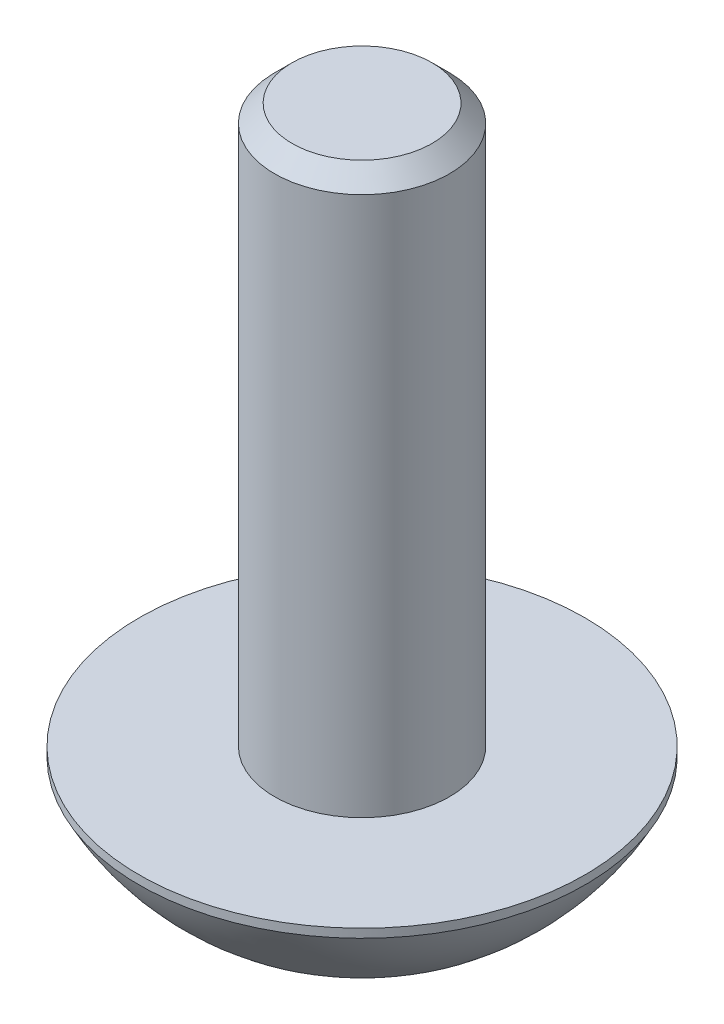
SolidWorks part; units mm, degrees
material "1.4301 (X5CrNi18-10)"
ref_plane "Vorderseite" through (0, 0, 0) normal (0, 0, 1) x (1, 0, 0)
ref_plane "Oben" through (0, 0, 0) normal (0, 1, 0) x (1, 0, 0)
ref_plane "Rechts" through (0, 0, 0) normal (1, 0, 0) x (0, 0, -1)
sketch "Skizze1" plane through (0, 0, 0) normal (0, 0, 1) x (1, 0, 0)
  line L0 (0, 12.3) -> (1.2564, 12.3)
  line L1 (1.2564, 12.3) -> (1.5705, 11.9859)
  line L2 (1.5705, 2.3) -> (1.5705, 11.9859)
  line L3 (1.5705, 2.3) -> (4, 2.3)
  line L7 (1.6004, 0) -> (1.4434, 0)
  line L8 (1.4434, 0) -> (1.2375, 0.2059)
  line L9 (1.2375, 0.2059) -> (1.2375, 1.4375)
  line L10 (1.2375, 1.4375) -> (0, 2.1811)
  line L11 (0, 2.1811) -> (0, 12.3)
  line L12 (0, 0) -> (0, 12.3) construction
  line L13 (4, 2.3) -> (4, 2.143)
  arc A1 (1.6004, 0) -> (4, 2.143) centre (0, 4.207) ccw
revolve "Basis-Rotation" add sketch "Skizze1" angle 360 about L12
sketch "Skizze2" plane through (0, 0, 0) normal (0, 1, 0) x (1, 0, 0)
  line L0 (-0.7217, -1.25) -> (0.7217, -1.25)
  line L1 (0.7217, -1.25) -> (1.4434, 0)
  line L2 (0.7217, 1.25) -> (1.4434, 0)
  line L3 (-0.7217, 1.25) -> (0.7217, 1.25)
  line L4 (-0.7217, 1.25) -> (-1.4434, 0)
  line L5 (-0.7217, -1.25) -> (-1.4434, 0)
  line L6 (0, 1.25) -> (0, -1.25) construction
  line L7 (-1.4434, 0) -> (1.4434, 0) construction
  point P3 (0, 1.25)
  point P5 (0, -1.25)
  dimension "D1" = 120
  dimension "S" = 2.5
extrude "Schnitt-Linear austragen1" cut sketch "Skizze2" along normal blind 1.4375
equation "\"Anplanung und zyl. Kopf@Skizze1\" = \"DG@Skizze1\"*0.05"
